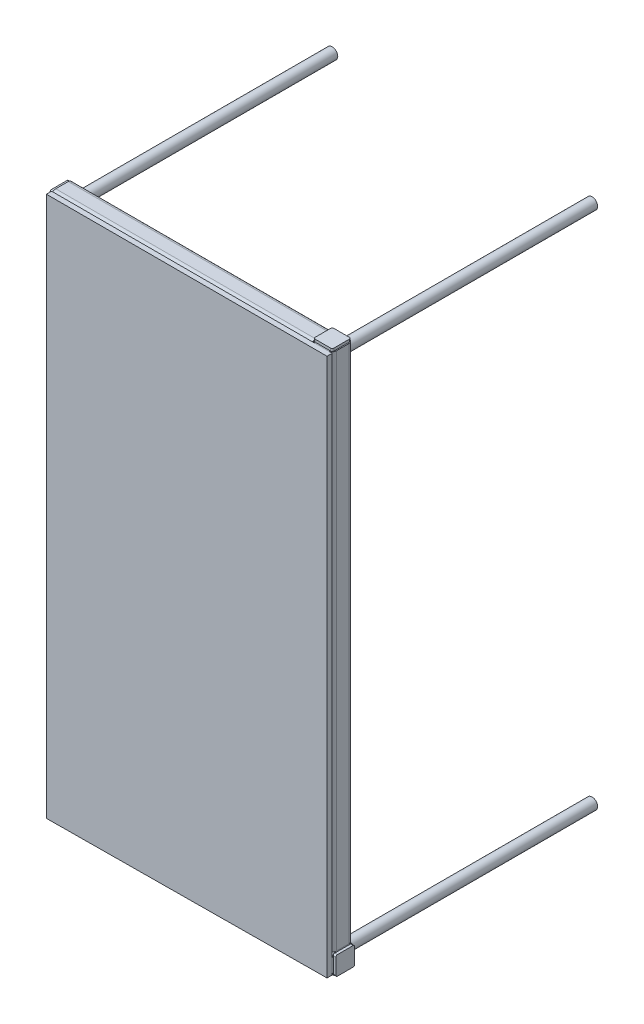
SolidWorks part; units mm, degrees
ref_plane "Front Plane" through (0, 0, 0) normal (0, 0, 1) x (1, 0, 0)
ref_plane "Top Plane" through (0, 0, 0) normal (0, 1, 0) x (1, 0, 0)
ref_plane "Right Plane" through (0, 0, 0) normal (1, 0, 0) x (0, 0, -1)
sketch3d "3DSketch1"
  line L0 (-250, -500, 0) -> (-250, -500, -500)
  line L1 (-250, 500, 0) -> (250, 500, 0)
  line L2 (-250, 500, 0) -> (-250, -500, 0)
  line L3 (-250, -500, 0) -> (250, -500, 0)
  line L4 (250, 500, 0) -> (250, -500, 0)
  line L5 (-250, 500, 0) -> (250, -500, 0) construction
  line L6 (-250, -500, 0) -> (250, 500, 0) construction
  line L7 (250, -500, 0) -> (250, -500, -500)
  line L8 (250, 500, 0) -> (250, 500, -500)
  line L9 (-250, 500, 0) -> (-250, 500, -500)
  point P0 (0, 0, 0)
  dimension "D1" = 1000
  dimension "D2" = 500
  dimension "D3" = 500
other "Structural Member1"
ref_plane "Plane1" through (-250, 500, 0) normal (0, -1, 0) x (1, 0, 0)
sketch "Sketch1" plane through (-250, 500, 0) normal (0, -1, 0) x (1, 0, 0)
  line L0 (-12, -16) -> (12, -16)
  line L1 (-16, -12) -> (-16, 12)
  line L2 (12, 16) -> (-12, 16)
  line L3 (16, 12) -> (16, -12)
  line L4 (-12, -20) -> (12, -20)
  line L5 (-20, -12) -> (-20, 12)
  line L6 (12, 20) -> (-12, 20)
  line L7 (20, 12) -> (20, -12)
  arc A0 (20, 12) -> (12, 20) centre (12, 12) ccw
  arc A1 (12, -20) -> (20, -12) centre (12, -12) ccw
  arc A2 (-20, -12) -> (-12, -20) centre (-12, -12) ccw
  arc A3 (-12, 20) -> (-20, 12) centre (-12, 12) ccw
  arc A4 (-12, 16) -> (-16, 12) centre (-12, 12) ccw
  arc A5 (16, 12) -> (12, 16) centre (12, 12) ccw
  arc A6 (12, -16) -> (16, -12) centre (12, -12) ccw
  arc A7 (-16, -12) -> (-12, -16) centre (-12, -12) ccw
  point P0 (-20, 0)
  point P1 (20, 0)
  point P2 (0, 20)
  point P3 (0, -20)
  point P4 (0, 0)
  point P5 (-20, -20)
  point P6 (20, -20)
  point P7 (20, 20)
  point P8 (-20, 20)
  point P33 (0, 0)
  dimension "D1" = 8
  dimension "Thickness" = 4
  dimension "V_leg" = 40
other "Structural Member2"
ref_plane "Plane2" through (-250, -500, 0) normal (0, 0, -1) x (1, 0, 0)
sketch "Sketch11" plane through (-250, -500, 0) normal (0, 0, -1) x (1, 0, 0)
  circle A0 centre (0, 0) radius 8.35
  circle A1 centre (0, 0) radius 10.65
  point P3 (0, 0)
  dimension "In_dia" = 16.7
  dimension "Out_dia" = 21.3
other "Trim/Extend1"
other "End cap1" parameters "D1"=5, "D2"=3, "D3"=3, "D4"=0
other "Gusset1" parameters "D1"=5, "D2"=5, "D3"=0, "D4"=0, "D10"=5, "D11"=25, "D12"=25, "D13"=15, "D14"=45, "D15"=15
sketch "Sketch12" plane through (-230, -480, 0) normal (0, 0, 1) x (1, 0, 0)
  line L0 (0, 0) -> (0, 25)
  line L1 (0, 0) -> (25, 0)
  line L2 (0, 25) -> (25, 0)
sketch "Sketch13" plane through (0, 0, 20) normal (0, 0, 1) x (1, 0, 0)
  line L0 (-270, -520) -> (270, -516)
  line L1 (270, -516) -> (270, 520)
  line L2 (270, 520) -> (-270, 520)
  line L3 (-270, 520) -> (-270, -520)
extrude "Boss-Extrude1" add sketch "Sketch13" along normal blind 10 separate body
other "End cap2" parameters "D1"=5, "D2"=3, "D3"=3, "D4"=0
other "End cap3" parameters "D1"=5, "D2"=3, "D3"=3, "D4"=0
other "End cap4" parameters "D1"=5, "D2"=3, "D3"=3, "D4"=0
